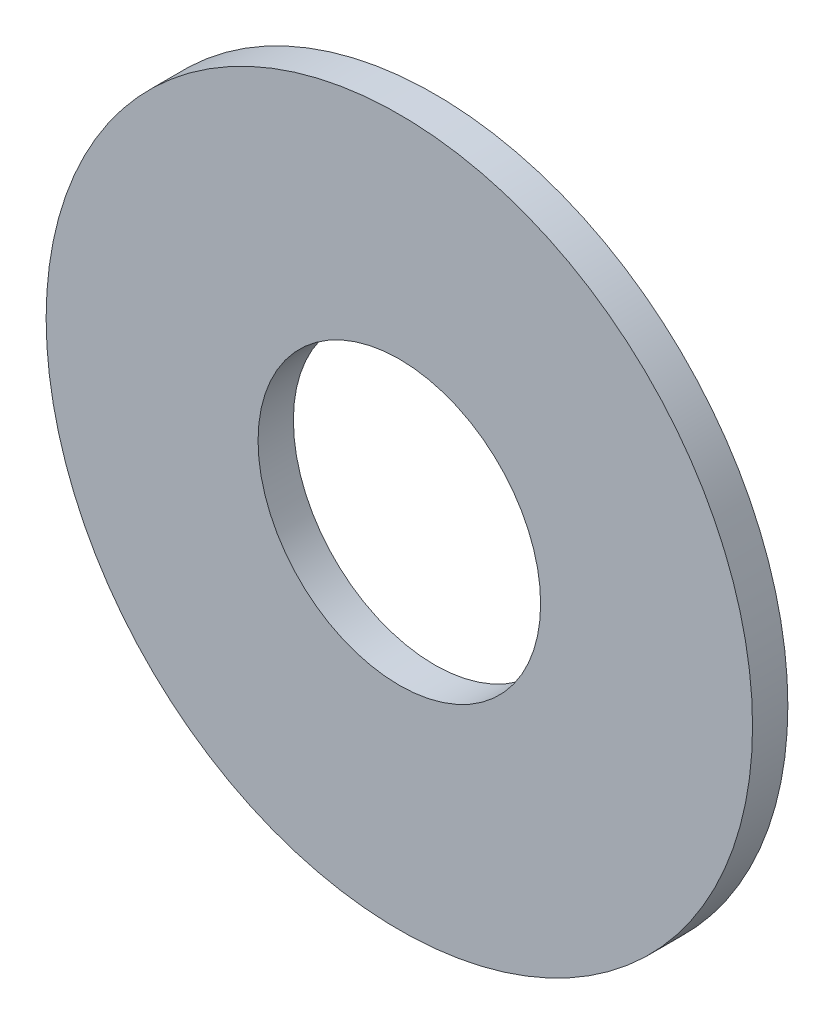
SolidWorks part; units mm, degrees
ref_plane "Спереди" through (0, 0, 0) normal (0, 0, 1) x (1, 0, 0)
ref_plane "Сверху" through (0, 0, 0) normal (0, 1, 0) x (1, 0, 0)
ref_plane "Справа" through (0, 0, 0) normal (1, 0, 0) x (0, 0, -1)
sketch "Эскиз1" plane through (0, 0, 0) normal (0, 0, 1) x (1, 0, 0)
  circle A0 centre (0, 0) radius 6
  circle A1 centre (0, 0) radius 15
  dimension "D1" = 12
  dimension "D2" = 30
extrude "Бобышка-Вытянуть1" add sketch "Эскиз1" along normal blind 1.5
